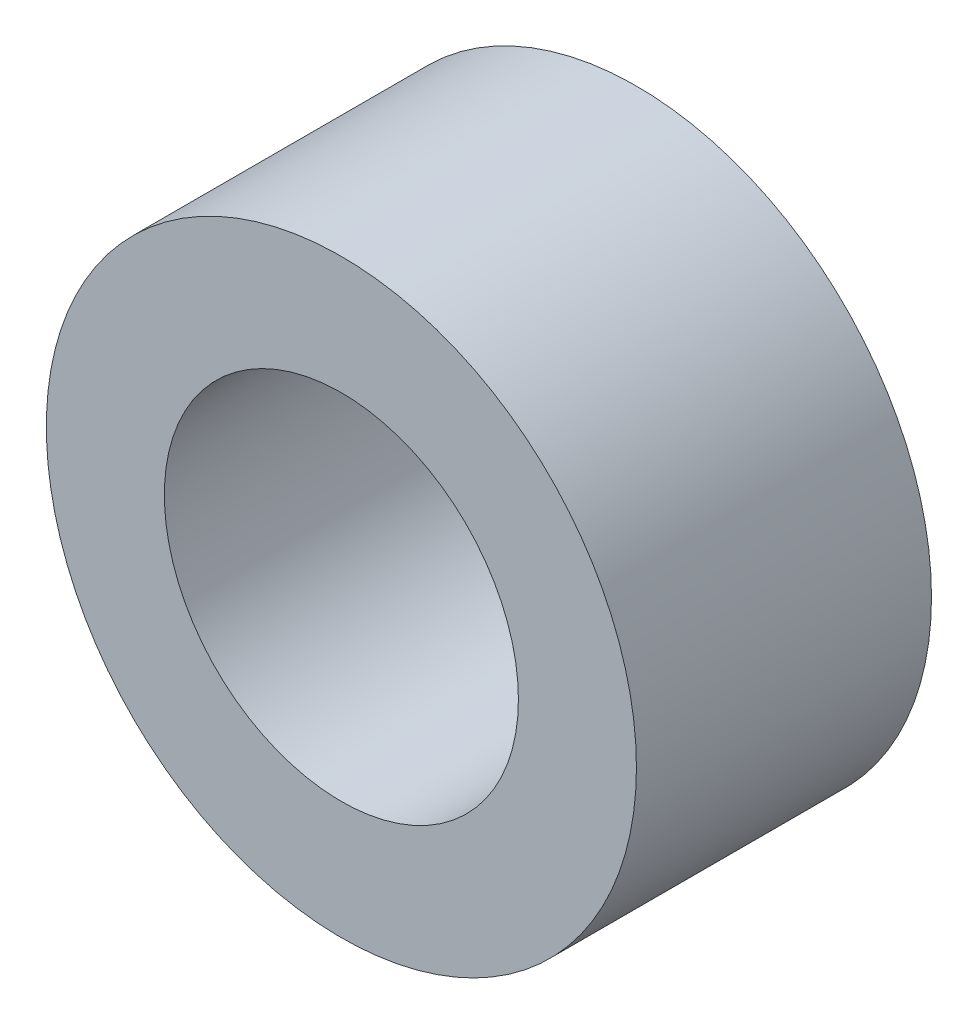
SolidWorks part; units mm, degrees
ref_plane "Plan de face" through (0, 0, 0) normal (0, 0, 1) x (1, 0, 0)
ref_plane "Plan de dessus" through (0, 0, 0) normal (0, 1, 0) x (1, 0, 0)
ref_plane "Plan de droite" through (0, 0, 0) normal (1, 0, 0) x (0, 0, -1)
sketch "Esquisse1" plane through (0, 0, 0) normal (0, 0, 1) x (1, 0, 0)
  circle A0 centre (0, 0) radius 1.2
  circle A1 centre (0, 0) radius 2
  dimension "D1" = 4
  dimension "D2" = 2.4
extrude "Boss.-Extru.1" add sketch "Esquisse1" along normal blind 2
